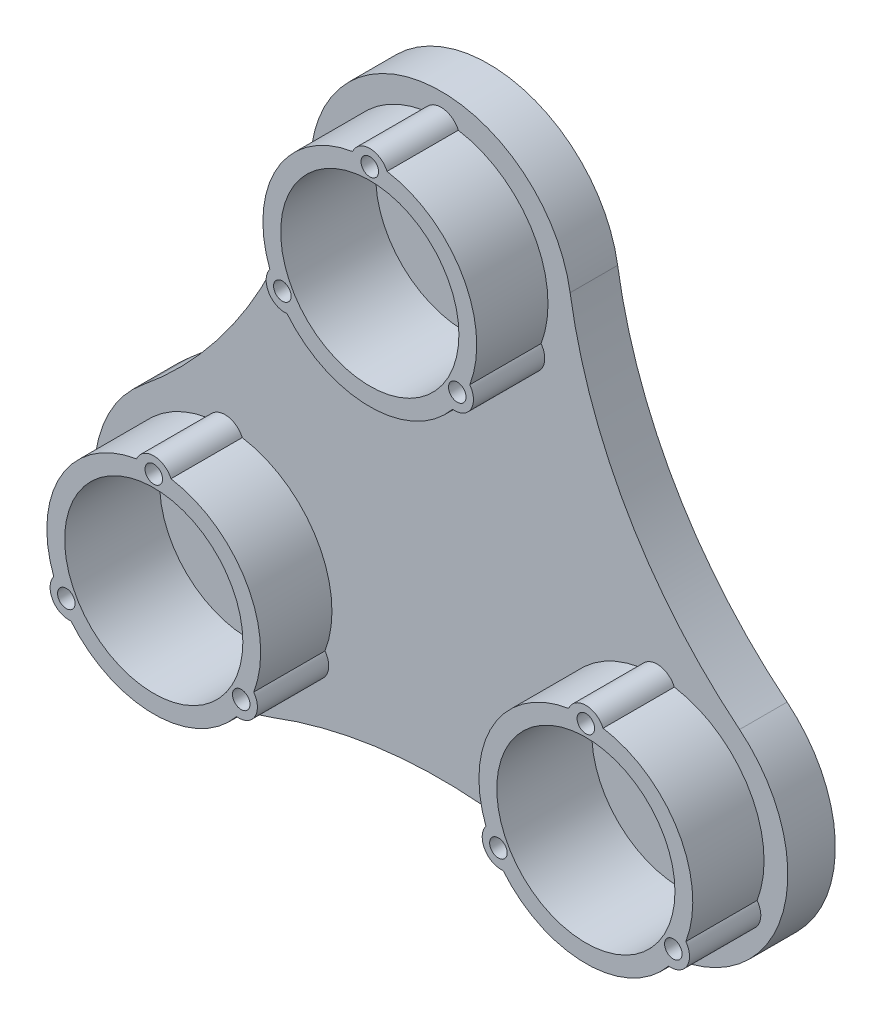
SolidWorks part; units mm, degrees
ref_plane "前视基准面" through (0, 0, 0) normal (0, 0, 1) x (1, 0, 0)
ref_plane "上视基准面" through (0, 0, 0) normal (0, 1, 0) x (1, 0, 0)
ref_plane "右视基准面" through (0, 0, 0) normal (1, 0, 0) x (0, 0, -1)
sketch "草图1" plane through (0, 0, 0) normal (0, 0, 1) x (1, 0, 0)
  circle A0 centre (0, 0) radius 15.75
  circle A1 centre (0, 0) radius 23 construction
  circle A3 centre (0, 0) radius 20
extrude "凸台-拉伸1" add sketch "草图1" along normal blind 5
sketch "草图2" plane through (0, 0, 5) normal (0, 0, 1) x (1, 0, 0)
  circle A0 centre (0, 0) radius 24 construction
  arc A2 (0, -25.8924) -> (22.4235, 12.9462) centre (20.7846, -12) ccw
  arc A3 (-22.4235, 12.9462) -> (0, -25.8924) centre (-20.7846, -12) ccw
  arc A5 (22.4235, 12.9462) -> (-22.4235, 12.9462) centre (0, 24) ccw
  point P12 (0, 0)
extrude "凸台-拉伸2" add sketch "草图2" along normal blind 8
sketch "草图3" plane through (0, 0, 13) normal (0, 0, 1) x (1, 0, 0)
  circle A0 centre (0, 42) radius 18
  circle A1 centre (36.3731, -21) radius 18
  circle A2 centre (-36.3731, -21) radius 18
  point P2 (0, 42)
  point P3 (0, 42)
  point P10 (0, 0)
  dimension "D1" = 3
  dimension "D3" = 42
extrude "凸台-拉伸3" add sketch "草图3" along normal blind 12
sketch "草图8" plane through (0, 0, 5) normal (0, 0, -1) x (-1, 0, 0)
  line L0 (0, 42) -> (36.3731, -21) construction
  line L1 (0, 0) -> (18.1865, 10.5) construction
  line L2 (18.1865, 10.5) -> (86.4245, 49.8972) construction
  line L3 (0, 0) -> (0, -8.0959) construction
  circle A0 centre (0, 0) radius 42 construction
  circle A4 centre (0, 42) radius 22
  circle A5 centre (36.3731, -21) radius 22
  circle A6 centre (-36.3731, -21) radius 22
  arc A7 (21.7226, 45.4827) -> (50.2505, -3.929) centre (100.7138, 58.1471) ccw
  arc A8 (-21.7226, 45.4827) -> (-50.2505, -3.929) centre (-100.7138, 58.1471) cw
  arc A9 (28.5279, -41.5537) -> (-28.5279, -41.5537) centre (0, -116.2943) ccw
  point P12 (0, 0)
  point P14 (0, 0)
  arc M7 (22.4235, 12.9462) -> (-22.4235, 12.9462) centre (0, 24) ccw
  arc M9 (-22.4235, 12.9462) -> (0, -25.8924) centre (-20.7846, -12) ccw
  arc M11 (0, -25.8924) -> (22.4235, 12.9462) centre (20.7846, -12) ccw
  dimension "D1" = 3
extrude "凸台-拉伸6" add sketch "草图8" against normal up to surface (8 mm away) contours A4 M7 | A7 A4 A5 M7 M11 | A5 M11 | A9 A5 A6 M11 M9 | A6 M9 | A4 A8 A6 M9 M7
sketch "草图4" plane through (0, 0, 25) normal (0, 0, 1) x (1, 0, 0)
  circle A0 centre (0, 42) radius 15
  circle A1 centre (36.3731, -21) radius 15
  circle A2 centre (-36.3731, -21) radius 15
  point P3 (36.3731, -21)
  point P10 (0, 0)
  dimension "D1" = 3
extrude "切除-拉伸1" cut sketch "草图4" against normal blind 16
sketch "草图6" plane through (0, 0, 25) normal (0, 0, 1) x (1, 0, 0)
  arc A7 (2.6444, 56.7651) -> (-2.6444, 56.7651) centre (0, 58.5) ccw
  arc A11 (2.6444, 56.7651) -> (-2.6444, 56.7651) centre (0, 42) ccw
  arc A12 (11.4647, 32.3274) -> (14.1091, 36.9075) centre (14.2894, 33.75) ccw
  arc A13 (11.4647, 32.3274) -> (14.1091, 36.9075) centre (0, 42) ccw
  arc A14 (-14.1091, 36.9075) -> (-11.4647, 32.3274) centre (-14.2894, 33.75) ccw
  arc A15 (-14.1091, 36.9075) -> (-11.4647, 32.3274) centre (0, 42) ccw
  arc A16 (47.8378, -30.6726) -> (50.4822, -26.0925) centre (50.6625, -29.25) ccw
  arc A17 (47.8378, -30.6726) -> (50.4822, -26.0925) centre (36.3731, -21) ccw
  arc A18 (22.264, -26.0925) -> (24.9083, -30.6726) centre (22.0836, -29.25) ccw
  arc A19 (22.264, -26.0925) -> (24.9083, -30.6726) centre (36.3731, -21) ccw
  arc A20 (39.0174, -6.2349) -> (33.7287, -6.2349) centre (36.3731, -4.5) ccw
  arc A21 (39.0174, -6.2349) -> (33.7287, -6.2349) centre (36.3731, -21) ccw
  arc A22 (-50.4822, -26.0925) -> (-47.8378, -30.6726) centre (-50.6625, -29.25) ccw
  arc A23 (-50.4822, -26.0925) -> (-47.8378, -30.6726) centre (-36.3731, -21) ccw
  arc A24 (-33.7287, -6.2349) -> (-39.0174, -6.2349) centre (-36.3731, -4.5) ccw
  arc A25 (-33.7287, -6.2349) -> (-39.0174, -6.2349) centre (-36.3731, -21) ccw
  arc A26 (-24.9083, -30.6726) -> (-22.264, -26.0925) centre (-22.0836, -29.25) ccw
  arc A27 (-24.9083, -30.6726) -> (-22.264, -26.0925) centre (-36.3731, -21) ccw
  point P1 (0, 0)
  point P14 (0, 42)
  point P25 (36.3731, -21)
  point P37 (-36.3731, -21)
  point P38 (0, 0)
  dimension "D1" = 3
  dimension "D2" = 16.5
sketch "草图7" plane through (0, 0, 9) normal (0, 0, 1) x (1, 0, 0)
  circle A0 centre (0, 42) radius 2
  circle A1 centre (36.3731, -21) radius 2
  circle A2 centre (-36.3731, -21) radius 2
  point P3 (36.3731, -21)
  point P9 (0, 0)
  dimension "D1" = 3
extrude "切除-拉伸2" cut sketch "草图7" against normal blind 10
extrude "凸台-拉伸7" add sketch "草图6" against normal up to next
sketch "草图9" plane through (0, 0, 25) normal (0, 0, 1) x (1, 0, 0)
  circle A0 centre (0, 42) radius 17 construction
  circle A1 centre (0, 59) radius 1.475
  circle A2 centre (14.7224, 33.5) radius 1.475
  circle A3 centre (-14.7224, 33.5) radius 1.475
  circle A4 centre (51.0955, -29.5) radius 1.475
  circle A5 centre (21.6506, -29.5) radius 1.475
  circle A6 centre (36.3731, -4) radius 1.475
  circle A7 centre (36.3731, -21) radius 17 construction
  circle A8 centre (-51.0955, -29.5) radius 1.475
  circle A9 centre (-36.3731, -4) radius 1.475
  circle A10 centre (-21.6506, -29.5) radius 1.475
  circle A11 centre (-36.3731, -21) radius 17 construction
  point P12 (0, 42)
  point P21 (36.3731, -21)
  point P30 (-36.3731, -21)
  point P31 (0, 0)
  dimension "D1" = 3
  dimension "D2" = 3
extrude "切除-拉伸3" cut sketch "草图9" against normal blind 5
ref_plane "基准面1" through (0, 0, 2.5) normal (0, 0, -1) x (-1, 0, 0)
sketch "草图10" plane through (0, 0, 2.5) normal (0, 0, -1) x (-1, 0, 0)
  line L0 (0, 26.5971) -> (0, -28.7314) construction
  line L1 (0, 23.6711) -> (1.475, 23.6711)
  line L2 (1.475, 23.6711) -> (1.475, -24.2093)
  line L3 (1.475, -24.2093) -> (0, -24.2093)
  line L4 (0, -24.2093) -> (0, 23.6711)
revolve "切除-旋转1" cut sketch "草图10" angle 360 about L0
sketch "草图11" plane through (0, 0, 2.5) normal (0, 0, -1) x (-1, 0, 0)
  line L0 (-35.3446, 0) -> (29.9106, 0) construction
  line L1 (-23.6643, 0) -> (-23.6643, 1.475)
  line L2 (-23.6643, 1.475) -> (24.1188, 1.475)
  line L3 (24.1188, 1.475) -> (24.1188, 0)
  line L4 (24.1188, 0) -> (-23.6643, 0)
revolve "切除-旋转2" cut sketch "草图11" angle 360 about L0
sketch "草图12" plane through (0, 0, 5) normal (0, 0, -1) x (-1, 0, 0)
  line L0 (0, 42) -> (0, 32) construction
  line L1 (0, 32) -> (6.5, 32)
  line L2 (6.5, 32) -> (6.5, 60)
  line L4 (-6.5, 60) -> (-6.5, 32)
  line L5 (-6.5, 32) -> (0, 32)
  line L6 (6.5, 32) -> (6.5, 60)
  line L7 (6.5, 60) -> (-6.5, 60)
  line L8 (27.7128, -16) -> (24.4628, -21.6292)
  line L9 (24.4628, -21.6292) -> (48.7115, -35.6292)
  line L10 (55.2115, -24.3708) -> (30.9628, -10.3708)
  line L11 (30.9628, -10.3708) -> (27.7128, -16)
  line L12 (24.4628, -21.6292) -> (48.7115, -35.6292)
  line L13 (48.7115, -35.6292) -> (55.2115, -24.3708)
  line L14 (36.3731, -21) -> (27.7128, -16) construction
  line L15 (-27.7128, -16) -> (-30.9628, -10.3708)
  line L16 (-30.9628, -10.3708) -> (-55.2115, -24.3708)
  line L17 (-48.7115, -35.6292) -> (-24.4628, -21.6292)
  line L18 (-24.4628, -21.6292) -> (-27.7128, -16)
  line L19 (-30.9628, -10.3708) -> (-55.2115, -24.3708)
  line L20 (-55.2115, -24.3708) -> (-48.7115, -35.6292)
  line L21 (-36.3731, -21) -> (-27.7128, -16) construction
  point P22 (0, 0)
  dimension "D1" = 10
  dimension "D2" = 28
  dimension "D3" = 13
extrude "切除-拉伸4" cut sketch "草图12" against normal blind 1.5
